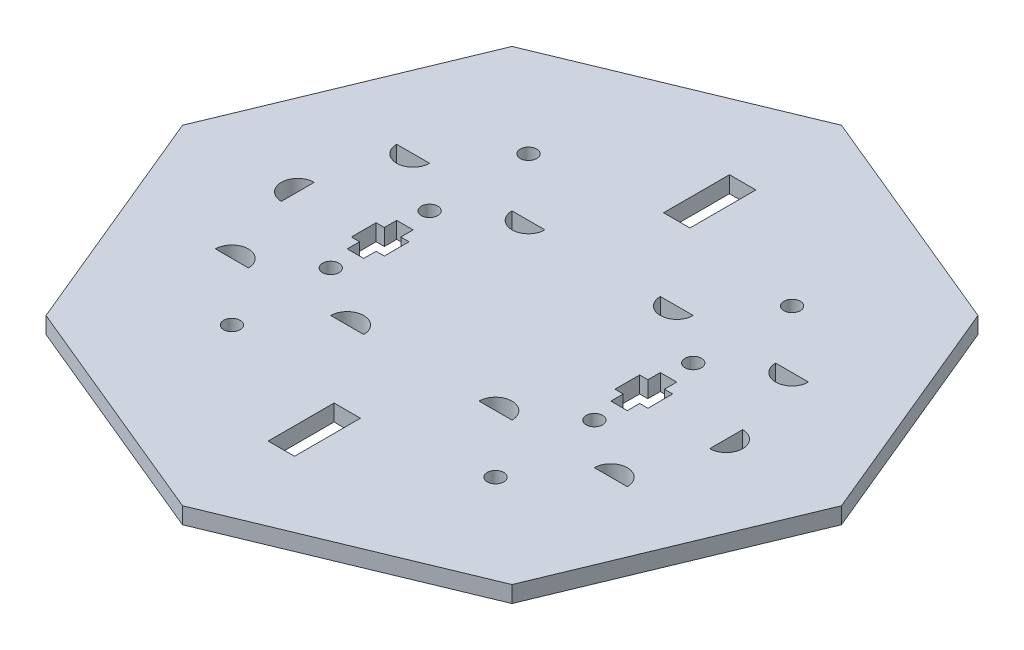
SolidWorks part; units mm, degrees
material "Ceramic Porcelain"
ref_plane "Front Plane" through (0, 0, 0) normal (0, 0, 1) x (1, 0, 0)
ref_plane "Top Plane" through (0, 0, 0) normal (0, 1, 0) x (1, 0, 0)
ref_plane "Right Plane" through (0, 0, 0) normal (1, 0, 0) x (0, 0, -1)
ref_plane "Plane1" through (0, 0, 0) normal (0, 1, 0) x (1, 0, 0)
sketch "Sketch1" plane through (0, 0, 0) normal (0, 1, 0) x (1, 0, 0)
  line L0 (-7.0711, 7.0711) -> (0, 10)
  line L1 (0, 10) -> (7.0711, 7.0711)
  line L2 (7.0711, 7.0711) -> (10, 0)
  line L3 (10, 0) -> (7.0711, -7.0711)
  line L4 (7.0711, -7.0711) -> (0, -10)
  line L5 (0, -10) -> (-7.0711, -7.0711)
  line L6 (-7.0711, -7.0711) -> (-10, 0)
  line L7 (-10, 0) -> (-7.0711, 7.0711)
  line L8 (-0.4, 7) -> (0.4, 7)
  line L9 (0.4, 7) -> (0.4, 5)
  line L10 (0.4, 5) -> (-0.4, 5)
  line L11 (-0.4, 5) -> (-0.4, 7)
  line L12 (-0.4, -5) -> (0.4, -5)
  line L13 (0.4, -5) -> (0.4, -7)
  line L14 (0.4, -7) -> (-0.4, -7)
  line L15 (-0.4, -7) -> (-0.4, -5)
  circle A0 centre (-4, 4.5) radius 0.25
  circle A1 centre (4, 4.5) radius 0.25
  circle A2 centre (4, -4.5) radius 0.25
  circle A3 centre (-4, -4.5) radius 0.25
extrude "Extrude1" add sketch "Sketch1" along normal blind 0.5
ref_plane "Plane2" through (0, 0, 0) normal (0, 1, 0) x (1, 0, 0)
sketch "Sketch2" plane through (0, 0, 0) normal (0, 1, 0) x (1, 0, 0)
  line L0 (3.75, 0.75) -> (4.25, 0.75)
  line L1 (4.5, 0.375) -> (4.5, -0.375)
  line L2 (4.25, -0.75) -> (3.75, -0.75)
  line L3 (3.5, -0.375) -> (3.5, 0.375)
  line L4 (4.25, 0.75) -> (4.25, 0.375)
  line L5 (4.25, 0.375) -> (4.5, 0.375)
  line L6 (3.75, 0.75) -> (3.75, 0.375)
  line L7 (3.75, 0.375) -> (3.5, 0.375)
  line L8 (4.25, -0.75) -> (4.25, -0.375)
  line L9 (4.25, -0.375) -> (4.5, -0.375)
  line L10 (3.75, -0.75) -> (3.75, -0.375)
  line L11 (3.75, -0.375) -> (3.5, -0.375)
  line L12 (-3.5, 0.375) -> (-3.5, -0.375)
  line L13 (-3.5, -0.375) -> (-3.75, -0.375)
  line L14 (-3.75, -0.375) -> (-3.75, -0.75)
  line L15 (-3.75, -0.75) -> (-4.25, -0.75)
  line L16 (-4.25, -0.75) -> (-4.25, -0.375)
  line L17 (-4.25, -0.375) -> (-4.5, -0.375)
  line L18 (-4.5, -0.375) -> (-4.5, 0.375)
  line L19 (-4.5, 0.375) -> (-4.25, 0.375)
  line L20 (-4.25, 0.375) -> (-4.25, 0.75)
  line L21 (-4.25, 0.75) -> (-3.75, 0.75)
  line L22 (-3.75, 0.75) -> (-3.75, 0.375)
  line L23 (-3.75, 0.375) -> (-3.5, 0.375)
  line L24 (-6.5, 0.5) -> (-6.5, -0.5)
  line L25 (6.5, 0.5) -> (6.5, -0.5)
  line L26 (-6.25, 2.75) -> (-5.25, 2.75)
  line L27 (-2.75, 2.75) -> (-1.75, 2.75)
  line L28 (1.75, 2.75) -> (2.75, 2.75)
  line L29 (5.25, 2.75) -> (6.25, 2.75)
  line L30 (-6.25, -2.75) -> (-5.25, -2.75)
  line L31 (-2.75, -2.75) -> (-1.75, -2.75)
  line L32 (1.75, -2.75) -> (2.75, -2.75)
  line L33 (5.25, -2.75) -> (6.25, -2.75)
  circle A0 centre (4, 1.5) radius 0.25
  circle A1 centre (4, -1.5) radius 0.25
  circle A2 centre (-4, 1.5) radius 0.25
  circle A3 centre (-4, -1.5) radius 0.25
  arc A4 (-6.5, 0.5) -> (-6.5, -0.5) centre (-6.5, 0) ccw
  arc A5 (6.5, -0.5) -> (6.5, 0.5) centre (6.5, 0) ccw
  arc A6 (5.25, 2.75) -> (6.25, 2.75) centre (5.75, 2.75) ccw
  arc A7 (1.75, 2.75) -> (2.75, 2.75) centre (2.25, 2.75) ccw
  arc A8 (-2.75, 2.75) -> (-1.75, 2.75) centre (-2.25, 2.75) ccw
  arc A9 (-6.25, 2.75) -> (-5.25, 2.75) centre (-5.75, 2.75) ccw
  arc A10 (6.25, -2.75) -> (5.25, -2.75) centre (5.75, -2.75) ccw
  arc A11 (2.75, -2.75) -> (1.75, -2.75) centre (2.25, -2.75) ccw
  arc A12 (-1.75, -2.75) -> (-2.75, -2.75) centre (-2.25, -2.75) ccw
  arc A13 (-5.25, -2.75) -> (-6.25, -2.75) centre (-5.75, -2.75) ccw
  dimension "D1" = 1.5
  dimension "D2" = 1.5
extrude "Extrude2" cut sketch "Sketch2" along normal through all
